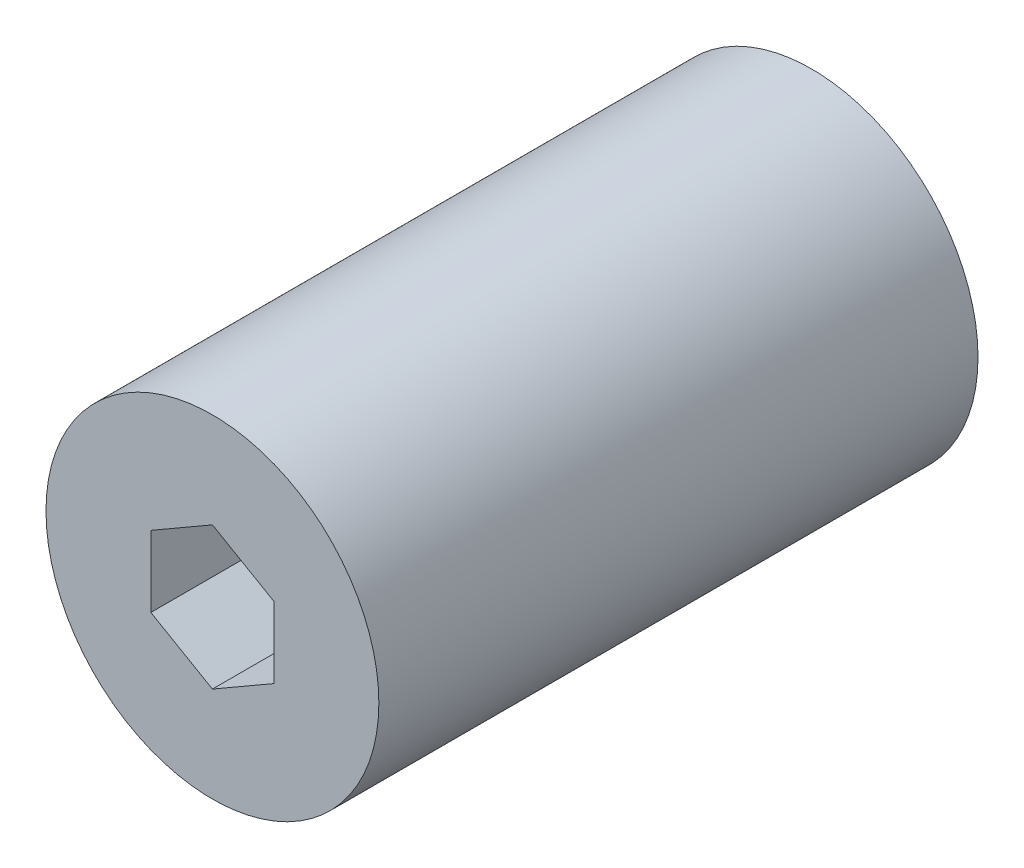
SolidWorks part; units mm, degrees
ref_plane "Plano frontal" through (0, 0, 0) normal (0, 0, 1) x (1, 0, 0)
ref_plane "Plano superior" through (0, 0, 0) normal (0, 1, 0) x (1, 0, 0)
ref_plane "Plano direito" through (0, 0, 0) normal (1, 0, 0) x (0, 0, -1)
sketch "Esboço2" plane through (0, 0, 0) normal (0, 0, 1) x (1, 0, 0)
  circle A0 centre (0, 0) radius 10
extrude "Ressalto-extrusão1" add sketch "Esboço2" along normal blind 36
sketch "Esboço3" plane through (0, 0, 36) normal (0, 0, 1) x (1, 0, 0)
  circle A0 centre (0, 0) radius 1.6
extrude "Corte-extrusão1" cut sketch "Esboço3" against normal up to next
sketch "Esboço4" plane through (0, 0, 36) normal (0, 0, 1) x (1, 0, 0)
  line L1 (0, 4.2724) -> (-3.7, 2.1362)
  line L2 (-3.7, 2.1362) -> (-3.7, -2.1362)
  line L3 (-3.7, -2.1362) -> (0, -4.2724)
  line L4 (0, -4.2724) -> (3.7, -2.1362)
  line L5 (3.7, -2.1362) -> (3.7, 2.1362)
  line L6 (3.7, 2.1362) -> (0, 4.2724)
  circle A0 centre (0, 0) radius 3.7 construction
extrude "Corte-extrusão2" cut sketch "Esboço4" against normal blind 15
